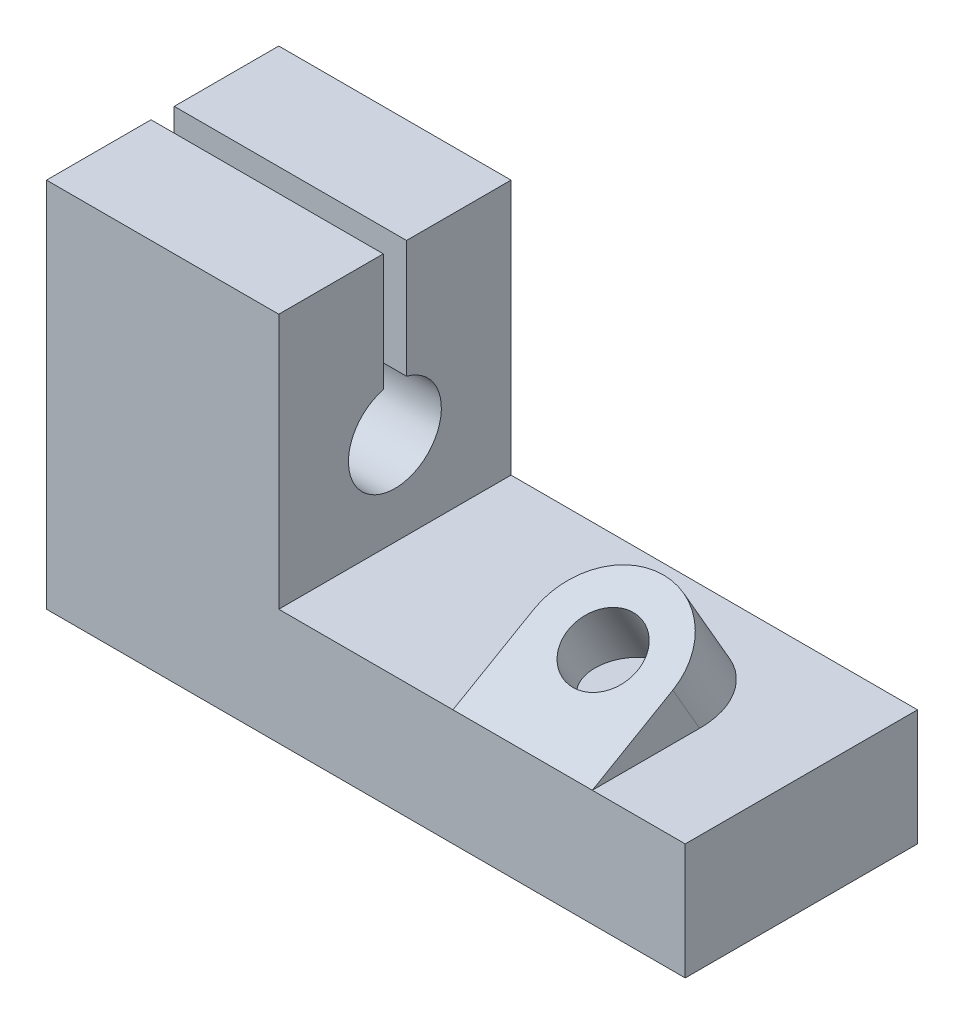
SolidWorks part; units mm, degrees
material "AISI 1020"
ref_plane "Front Plane" through (0, 0, 0) normal (0, 0, 1) x (1, 0, 0)
ref_plane "Top Plane" through (0, 0, 0) normal (0, 1, 0) x (1, 0, 0)
ref_plane "Right Plane" through (0, 0, 0) normal (1, 0, 0) x (0, 0, -1)
sketch "Sketch1" plane through (0, 0, 0) normal (0, 0, 1) x (1, 0, 0)
  line L0 (0, 0) -> (55, 0)
  line L1 (0, 0) -> (0, 32)
  line L2 (0, 32) -> (20, 32)
  line L3 (20, 32) -> (20, 10)
  line L4 (20, 10) -> (55, 10)
  line L5 (55, 10) -> (55, 0)
  dimension "D1" = 55
  dimension "D2" = 32
  dimension "D3" = 20
  dimension "D4" = 10
extrude "Boss-Extrude1" add sketch "Sketch1" along normal mid plane 20
sketch "Sketch2" plane through (20, 0, 0) normal (1, 0, 0) x (0, 0, -1)
  line L0 (0, 0) -> (0, 26.2776) construction
  line L1 (-10, 32) -> (10, 32) construction
  line L3 (-1, 32) -> (1, 32)
  line L4 (-1, 32) -> (-1, 21.873)
  line L6 (1, 32) -> (1, 21.873)
  arc A0 (-1, 21.873) -> (1, 21.873) centre (0, 18) ccw
  dimension "D1" = 4
  dimension "D2" = 14
  dimension "D3" = 2
extrude "Cut-Extrude1" cut sketch "Sketch2" against normal through all
ref_plane "Plane1" through (0, 11.8301, 6.8301) normal (0, 0.866, 0.5) x (-1, 0, 0)
sketch "Sketch3" plane through (0, 11.8301, 6.8301) normal (0, 0.866, 0.5) x (-1, 0, 0)
  line L0 (-55, 3.6603) -> (-20, 3.6603) construction
  line L1 (-47, 3.6603) -> (-35, 3.6603)
  line L2 (-47, 3.6603) -> (-47, -4.3397)
  line L4 (-35, 3.6603) -> (-35, -4.3397)
  line L5 (-20, 3.6603) -> (-20, -13.6603) construction
  arc A0 (-47, -4.3397) -> (-35, -4.3397) centre (-41, -4.3397) ccw
  circle A1 centre (-41, -4.3397) radius 3
  dimension "D1" = 6
  dimension "D3" = 6
  dimension "D2" = 15
  dimension "D4" = 8
extrude "Boss-Extrude2" add sketch "Sketch3" against normal up to next
